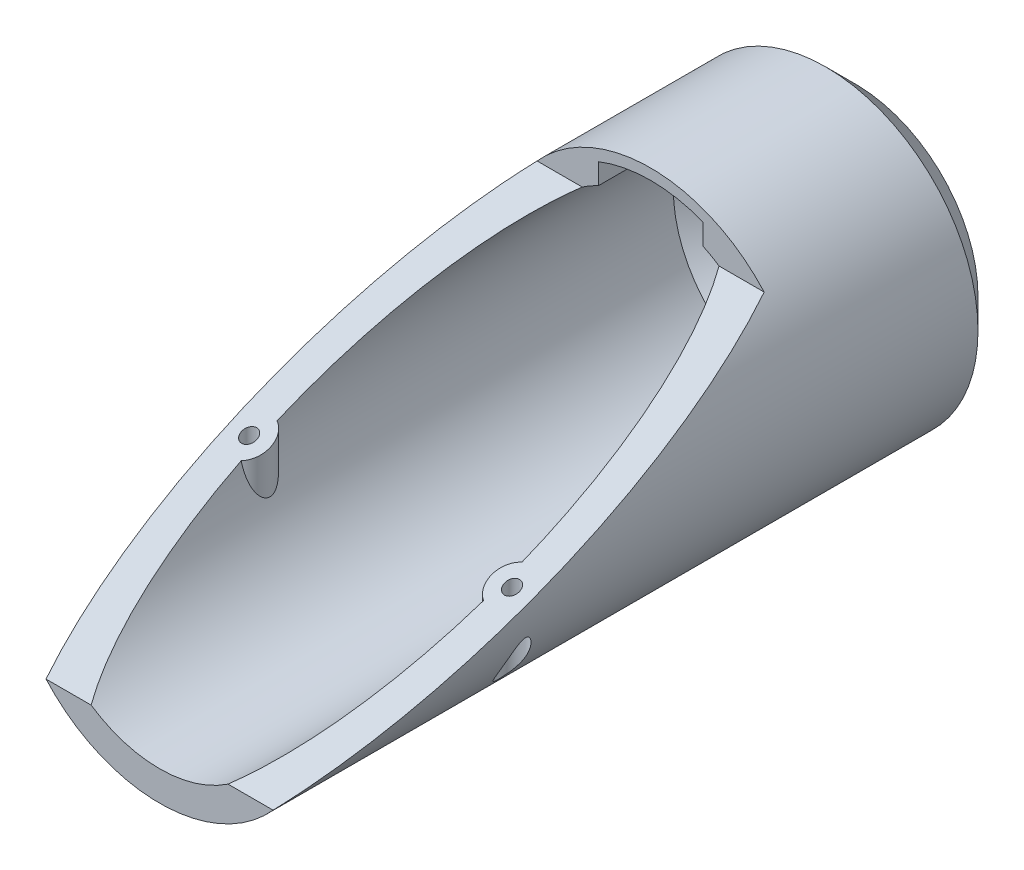
SolidWorks part; units mm, degrees
material "6061-T6 (SS)"
ref_plane "Front Plane" through (0, 0, 0) normal (0, 0, 1) x (1, 0, 0)
ref_plane "Top Plane" through (0, 0, 0) normal (0, 1, 0) x (1, 0, 0)
ref_plane "Right Plane" through (0, 0, 0) normal (1, 0, 0) x (0, 0, -1)
sketch "Sketch1" plane through (0, 0, 0) normal (0, 0, 1) x (1, 0, 0)
  circle A0 centre (0, 0) radius 25.5
  dimension "D1" = 51
extrude "Boss-Extrude1" add sketch "Sketch1" along normal blind 125
ref_plane "Plane2" through (0, -25.5, 0) normal (0, -1, 0) x (-1, 0, 0)
sketch "Sketch2" plane through (0, 0, 125) normal (0, 0, 1) x (1, 0, 0)
  circle A0 centre (0, 0) radius 20.5
  circle A1 centre (0, 0) radius 25.5 construction
  dimension "D1" = 5
extrude "Cut-Extrude1" cut sketch "Sketch2" against normal offset from surface (120 mm away) 5 up to face at (25.5, 0, 0)
ref_plane "Plane1" through (-25.5, 0, 0) normal (-1, 0, 0) x (0, 0, 1)
ref_plane "Plane4" through (0, 25.5, 0) normal (0, 1, 0) x (1, 0, 0)
sketch "Sketch8" plane through (0, 25.5, 0) normal (0, 1, 0) x (1, 0, 0)
  line L0 (0, 0) -> (0, -125.0325) construction
  line L1 (25.5, 0) -> (-25.5, 0) construction
  circle A0 centre (22, -79.5) radius 3.5
  circle A1 centre (-22, -79.5) radius 3.5
  dimension "D3" = 7
  dimension "D1" = 79.5
  dimension "D2" = 22
extrude "Boss-Extrude2" add sketch "Sketch8" against normal blind 42 contours A0
sketch "Sketch9" plane through (0, 0, 125) normal (0, 0, 1) x (1, 0, 0)
  circle A0 centre (0, 0) radius 25.5
  circle A1 centre (0, 0) radius 40.6837
extrude "Cut-Extrude7" cut sketch "Sketch9" against normal through all
sketch "Sketch3" plane through (-25.5, 0, 0) normal (-1, 0, 0) x (0, 0, 1)
  line L0 (116.5, -17) -> (34.3, 17)
  line L1 (34.3, 17) -> (34.3, 25.5)
  line L2 (34.3, 25.5) -> (125, 25.5)
  line L3 (125, -25.5) -> (125, 25.5) construction
  line L4 (125, 25.5) -> (125, -25.5)
  line L5 (125, -25.5) -> (116.5, -25.5)
  line L6 (116.5, -25.5) -> (116.5, -17)
  point P6 (125, -25.5)
  dimension "D1" = 8.5
  dimension "D2" = 8.5
  dimension "D3" = 82.2
extrude "Cut-Extrude2" cut sketch "Sketch3" against normal through all
sketch "Sketch10" plane through (0, 25.5, 0) normal (0, 1, 0) x (1, 0, 0)
  circle A0 centre (-22, -79.5) radius 1.25
  circle A1 centre (22, -79.5) radius 1.25
  dimension "D1" = 2.5
extrude "Cut-Extrude9" cut sketch "Sketch10" against normal through all
sketch "Sketch7" plane through (0, 0, 5) normal (0, 0, 1) x (1, 0, 0)
  circle A0 centre (0, 0) radius 21.5
  arc A1 (19.0066, -17) -> (19.0066, 17) centre (0, 0) ccw construction
  dimension "D1" = 4
ref_plane "Plane3" through (0, -4, 0) normal (0, 1, 0) x (1, 0, 0)
chamfer "Chamfer2" distance 5 angle 45 2 edges at (25.5, 0, 0) (20.5, 0, 5)
sketch "Sketch11" plane through (0, -4, 0) normal (0, 1, 0) x (1, 0, 0)
  circle A0 centre (-22, -79.5) radius 2.25
  circle A1 centre (22, -79.5) radius 2.25
  dimension "D1" = 4.5
extrude "Cut-Extrude10" cut sketch "Sketch11" against normal through all
sketch "Sketch12" plane through (0, 0, 116.5) normal (0, 0, 1) x (1, 0, 0)
  line L0 (-8.75, 22.0256) -> (-8.75, 18.5388)
  line L1 (8.75, 22.0256) -> (8.75, 18.5388)
  arc A0 (-8.75, 22.0256) -> (8.75, 22.0256) centre (0, 0) cw
  arc A1 (19.0066, 17) -> (-19.0066, 17) centre (0, 0) ccw construction
  arc A2 (11.4564, 17) -> (-11.4564, 17) centre (0, 0) ccw construction
  arc A3 (-8.75, 18.5388) -> (8.75, 18.5388) centre (0, 0) cw
  point P13 (9.1397, 18.5388)
  dimension "D1" = 1.8
  dimension "D2" = 17.5
  dimension "D3" = 8.75
extrude "Cut-Extrude11" cut sketch "Sketch12" against normal up to surface (103.3 mm away) contours L0 A3 L1 A0
